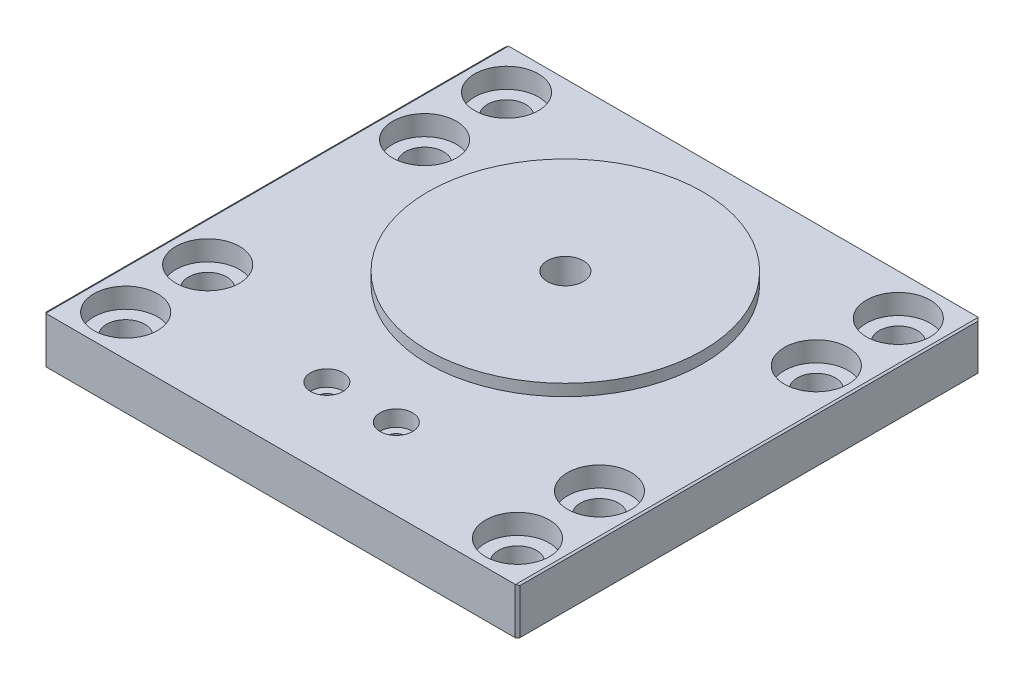
SolidWorks part; units mm, degrees
ref_plane "Front Plane" through (0, 0, 0) normal (0, 0, 1) x (1, 0, 0)
ref_plane "Top Plane" through (0, 0, 0) normal (0, 1, 0) x (1, 0, 0)
ref_plane "Right Plane" through (0, 0, 0) normal (1, 0, 0) x (0, 0, -1)
sketch "Sketch1" plane through (0, 0, 0) normal (0, 1, 0) x (1, 0, 0)
  line L1 (-104, 101.6) -> (0, 101.6)
  line L2 (-104, 101.6) -> (-104, 0)
  line L3 (-104, 0) -> (0, 0)
  line L4 (0, 101.6) -> (0, 0)
  dimension "D1" = 101.6
  dimension "D2" = 104
extrude "Boss-Extrude1" add sketch "Sketch1" along normal blind 10.16
sketch "Sketch5" plane through (0, 10.16, 0) normal (0, 1, 0) x (1, 0, 0)
  line L0 (0, 101.6) -> (-104, 101.6) construction
  line L2 (-52, 101.6) -> (-52, 0) construction
  line L3 (-104, 0) -> (0, 0) construction
  circle A0 centre (-52, 62.5094) radius 30.1625
  dimension "D1" = 39.0906
  dimension "D2" = 60.325
  dimension "D3" = 0
extrude "Boss-Extrude2" add sketch "Sketch5" along normal blind 2.54
hole_wizard "CBORE for #6 Socket Head Cap Screw1" positions "Sketch6" profile "Sketch8" counterbore size "#6" standard "ANSI Inch" end condition through all
sketch "Sketch6" plane through (0, 10.16, 0) normal (0, 1, 0) x (1, 0, 0)
  line L4 (-52, 0) -> (-52, 17.78) construction
  line L5 (-104, 0) -> (0, 0) construction
  line L9 (-52, 17.78) -> (-44.38, 17.78) construction
  line L11 (-52, 17.78) -> (-59.62, 17.78) construction
  point P116 (-59.62, 17.78)
  point P119 (-44.38, 17.78)
  dimension "D1" = 17.78
  dimension "D2" = 7.62
  dimension "D3" = 7.62
sketch "Sketch8" plane through (-44.38, 10.16, -17.78) normal (1, 0, 0) x (0, 0, 1)
  line L0 (0, 0) -> (0, 10.16)
  line L1 (0, 10.16) -> (1.8986, 10.16)
  line L3 (1.8986, 10.16) -> (1.8986, 3.5052)
  line L4 (1.8986, 3.5052) -> (3.5725, 3.5052)
  line L5 (3.5725, 3.5052) -> (3.5725, 0)
  line L7 (3.5725, 0) -> (0, 0)
  line L11 (0, -6.35) -> (0, 107.95) construction
  dimension "Thru Hole Dia." = 3.7973
  dimension "Thru Hole Depth" = 10.16
  dimension "C'Bore Dia." = 7.145
  dimension "C'Bore Depth" = 3.5052
hole_wizard "3/8-16 Tapped Hole1" positions "Sketch9" profile "Sketch11" tap size "3/8-16" standard "ANSI Inch" end condition through all
sketch "Sketch9" plane through (0, 12.7, 0) normal (0, 1, 0) x (1, 0, 0)
  point P0 (-52, 62.5094)
sketch "Sketch11" plane through (-52, 12.7, -62.5094) normal (1, 0, 0) x (0, 0, 1)
  line L0 (0, 0) -> (0, 12.7)
  line L1 (0, 12.7) -> (3.9687, 12.7)
  line L2 (3.9687, 12.7) -> (3.9687, 0)
  line L5 (3.9687, 0) -> (0, 0)
  line L11 (0, -6.35) -> (0, 107.95) construction
  dimension "Thread Major Dia." = 7.9375
  dimension "Thru Tap Drill Depth" = 12.7
thread "Thread1" pitch 0.7937 start angle 0, offset 0, length 0, pitch 0.7937, diameter 7.9375
ref_plane "Plane1" through (-55.9688, 12.7, -62.5094) normal (0, 0, 1) x (-1, 0, 0)
sketch "Thread Profile1" plane through (-55.9688, 12.7, -62.5094) normal (0, 0, 1) x (-1, 0, 0)
  line L0 (0, 0) -> (0, 0.7937) construction
  line L11 (0, 0) -> (0, 0.6945)
  line L12 (0, 0.6945) -> (-0.4296, 0.4465)
  line L13 (-0.4296, 0.4465) -> (-0.4296, 0.248)
  line L15 (-0.4296, 0.248) -> (0, 0)
  line L17 (-0.4296, 0.3473) -> (0, 0.3473) construction
  point P2 (0, 0)
  dimension "Pitch" = 0.7937
  dimension "Profile_Angle" = 60
  dimension "Profile_Land" = 0.1984
  dimension "Profile_Height" = 0.4296
hole_wizard "CBORE for M8 SBHCS1" positions "Sketch12" profile "Sketch13" counterbore size "M8" standard "ANSI Metric" end condition through all
sketch "Sketch12" plane through (0, 10.16, 0) normal (0, 1, 0) x (1, 0, 0)
  point P14 (-9, 92.6)
  point P17 (-9, 74.6)
  point P20 (-9, 27)
  point P23 (-9, 9)
  point P26 (-95, 9)
  point P29 (-95, 27)
  point P32 (-95, 74.6)
  point P35 (-95, 92.6)
sketch "Sketch13" plane through (-9, 10.16, -92.6) normal (1, 0, 0) x (0, 0, 1)
  line L0 (0, 0) -> (0, 10.16)
  line L1 (0, 10.16) -> (4.2, 10.16)
  line L3 (4.2, 10.16) -> (4.2, 4.4)
  line L4 (4.2, 4.4) -> (7, 4.4)
  line L5 (7, 4.4) -> (7, 0)
  line L7 (7, 0) -> (0, 0)
  line L11 (0, -6.35) -> (0, 107.95) construction
  dimension "Thru Hole Dia." = 8.4
  dimension "Thru Hole Depth" = 10.16
  dimension "C'Bore Dia." = 14
  dimension "C'Bore Depth" = 4.4
chamfer "Chamfer1" distance 0.254 angle 60 2 edges at (0, 10.16, -50.8) (-104, 10.16, -50.8)
chamfer "Chamfer2" distance 0.508 angle 45 4 edges at (0, 4.953, 0) (-104, 4.953, 0) (-104, 4.953, -101.6) (0, 4.953, -101.6)
